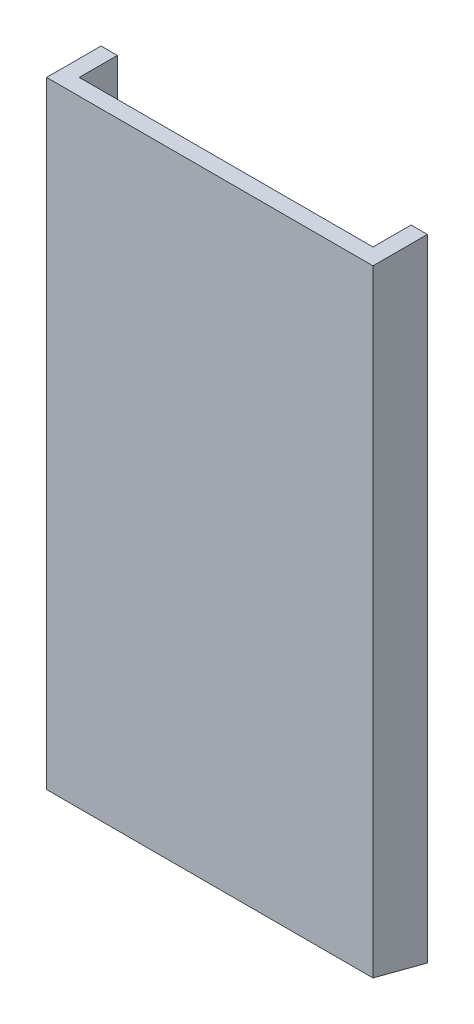
SolidWorks part; units mm, degrees
ref_plane "前视基准面" through (0, 0, 0) normal (0, 0, 1) x (1, 0, 0)
ref_plane "上视基准面" through (0, 0, 0) normal (0, 1, 0) x (1, 0, 0)
ref_plane "右视基准面" through (0, 0, 0) normal (1, 0, 0) x (0, 0, -1)
sketch "草图1" plane through (0, 0, 0) normal (0, 1, 0) x (1, 0, 0)
  line L0 (-15, 0) -> (15, 0)
  line L1 (15, 0) -> (15, 5)
  line L2 (13.5, 5) -> (15, 5)
  line L4 (13.5, 5) -> (13.5, 1.5)
  line L5 (13.5, 1.5) -> (-13.5, 1.5)
  line L6 (-13.5, 1.5) -> (-13.5, 5)
  line L7 (-13.5, 5) -> (-15, 5)
  line L8 (-15, 5) -> (-15, 0)
  dimension "D1" = 30
  dimension "D2" = 15
  dimension "D3" = 1.5
  dimension "D4" = 1.5
  dimension "D5" = 1.5
  dimension "D6" = 5
  dimension "D7" = 5
extrude "凸台-拉伸1" add sketch "草图1" along normal blind 58
sketch "草图2" plane through (-15, 0, 0) normal (-1, 0, 0) x (0, 0, 1)
  line L0 (-5, 58) -> (-5, 0) construction
  line L1 (-5, 12) -> (-13.364, 8.6395)
  line L2 (-5, 12) -> (-5, 0)
  line L3 (-11.5, -1) -> (-5, 0)
  arc A0 (-13.364, 8.6395) -> (-11.5, -1) centre (-11.5, 4) ccw
  dimension "D1" = 10
  dimension "D2" = 4
  dimension "D3" = 6.5
  dimension "D4" = 12
extrude "凸台-拉伸2" add sketch "草图2" against normal blind 1.5 separate body
sketch "草图3" plane through (-13.5, 0, 0) normal (1, 0, 0) x (0, 0, -1)
  circle A0 centre (11.5, 4) radius 1.55
extrude "切除-拉伸1" cut sketch "草图3" against normal blind 1.5
sketch "草图4" plane through (-15, 0, 0) normal (-1, 0, 0) x (0, 0, 1)
  line L0 (-5, 0) -> (0, 1.3051)
  line L1 (0, 58) -> (0, 0) construction
  line L2 (0, 1.3051) -> (0, 0)
  line L3 (0, 0) -> (-5, 0)
extrude "切除-拉伸2" cut sketch "草图4" against normal through all
